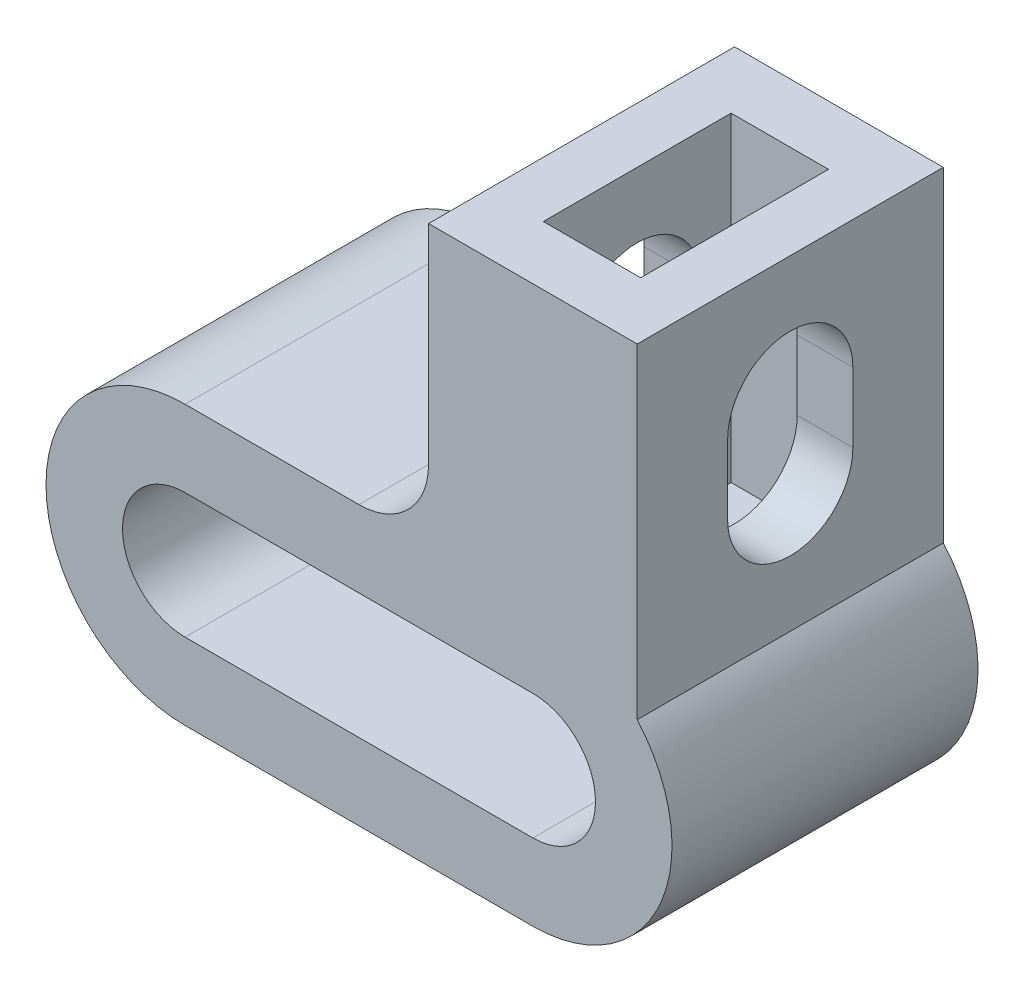
SolidWorks part; units mm, degrees
ref_plane "Plano frontal" through (0, 0, 0) normal (0, 0, 1) x (1, 0, 0)
ref_plane "Plano superior" through (0, 0, 0) normal (0, 1, 0) x (1, 0, 0)
ref_plane "Plano direito" through (0, 0, 0) normal (1, 0, 0) x (0, 0, -1)
sketch "Esboço1" plane through (0, 0, 0) normal (0, 0, 1) x (1, 0, 0)
  line L0 (0, 0) -> (0, 30) construction
  line L1 (7.5, 6.6144) -> (7.5, 30)
  line L2 (-7.5, 30) -> (7.5, 30)
  line L3 (-7.5, 15) -> (-7.5, 30)
  line L4 (7.5, 0) -> (7.5, 30) construction
  line L5 (-7.5, 0) -> (-7.5, 30) construction
  line L6 (0, 0) -> (-25, 0) construction
  line L7 (-25, 10) -> (-12.5, 10)
  line L8 (-25, -10) -> (0, -10)
  line L9 (-25, 4.5) -> (0, 4.5)
  line L10 (0, -4.5) -> (-25, -4.5)
  arc A0 (0, -4.5) -> (0, 4.5) centre (0, 0) ccw
  arc A1 (-12.5, 10) -> (-7.5, 15) centre (-12.5, 15) ccw
  arc A4 (-25, 10) -> (-25, -10) centre (-25, 0) ccw
  arc A5 (-25, 4.5) -> (-25, -4.5) centre (-25, 0) ccw
  arc A6 (0, -10) -> (7.5, 6.6144) centre (0, 0) ccw
  point P1 (7.13, 30)
  point P5 (7.0594, 7.0827)
  point P10 (7.5, 5.969)
  dimension "D1" = 9
  dimension "D2" = 5
  dimension "D5" = 10
  dimension "D3" = 30
  dimension "D7" = 25
  dimension "D4" = 15
extrude "Ressalto-extrusão1" add sketch "Esboço1" along normal blind 22
sketch "Esboço2" plane through (0, 30, 0) normal (0, 1, 0) x (1, 0, 0)
  line L0 (-7.5, -11) -> (7.5, -11) construction
  line L3 (7.5, -22) -> (7.5, 0) construction
  line L6 (-3.5, -4.25) -> (3.5, -4.25)
  line L7 (-3.5, -4.25) -> (-3.5, -17.75)
  line L8 (-3.5, -17.75) -> (3.5, -17.75)
  line L9 (3.5, -4.25) -> (3.5, -17.75)
  line L10 (-3.5, -4.25) -> (3.5, -17.75) construction
  line L11 (-3.5, -17.75) -> (3.5, -4.25) construction
  point P6 (0, -11)
  dimension "D1" = 7
  dimension "D2" = 13.5
extrude "Corte-extrusão1" cut sketch "Esboço2" against normal blind 23
sketch "Esboço3" plane through (7.5, 0, 0) normal (1, 0, 0) x (0, 0, -1)
  line L0 (0, 18.3072) -> (-22, 18.3072) construction
  line L1 (0, 6.6144) -> (0, 30) construction
  line L2 (-22, 6.6144) -> (-22, 30) construction
  line L3 (-11, 15.8072) -> (-11, 20.8072) construction
  line L4 (-15.5, 15.8072) -> (-15.5, 20.8072)
  line L5 (-6.5, 15.8072) -> (-6.5, 20.8072)
  arc A0 (-15.5, 15.8072) -> (-6.5, 15.8072) centre (-11, 15.8072) ccw
  arc A1 (-6.5, 20.8072) -> (-15.5, 20.8072) centre (-11, 20.8072) ccw
  point P8 (-11, 18.3072)
  dimension "D2" = 4.5
  dimension "D1" = 5
extrude "Corte-extrusão2" cut sketch "Esboço3" against normal blind 35 and the other way blind 10
